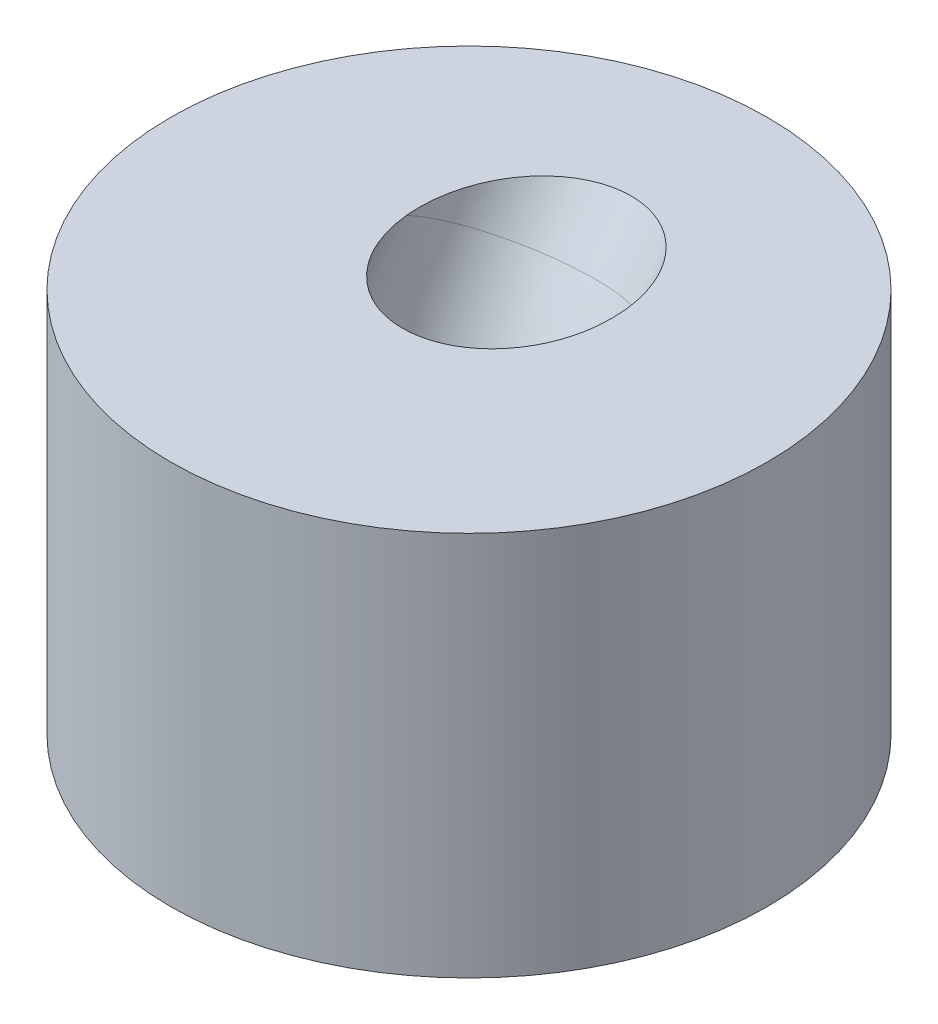
SolidWorks part; units mm, degrees
ref_plane "Front Plane" through (0, 0, 0) normal (0, 0, 1) x (1, 0, 0)
ref_plane "Top Plane" through (0, 0, 0) normal (0, 1, 0) x (1, 0, 0)
ref_plane "Right Plane" through (0, 0, 0) normal (1, 0, 0) x (0, 0, -1)
sketch "Sketch1" plane through (0, 0, 0) normal (0, 1, 0) x (1, 0, 0)
  circle A0 centre (0, 0) radius 0.775
  dimension "D1" = 1.55
extrude "Boss-Extrude1" add sketch "Sketch1" along normal blind 1 contours A0
sketch "Sketch2" plane through (0, 0, 0) normal (1, 0, 0) x (0, 0, -1)
  line L0 (-0.2221, -0.1527) -> (-0.2221, -0.128)
  line L1 (0.1149, 0.983) -> (0.3388, 1.3181)
  arc A0 (0.1149, 0.983) -> (-0.2221, -0.128) centre (1.7779, -0.128) ccw
  dimension "D1" = 2
sketch "Sketch3" plane through (0, 0, 0) normal (0, -1, 0) x (1, 0, 0)
  line L0 (0, -0.1149) -> (0, 0.2221) construction
  line L1 (0, -0.1149) -> (0, 0.2221) construction
  circle A0 centre (0, 0.2221) radius 0.25
  dimension "D1" = 0.5
sweep "Cut-Sweep1" cut profiles "Sketch3" path "Sketch2"
